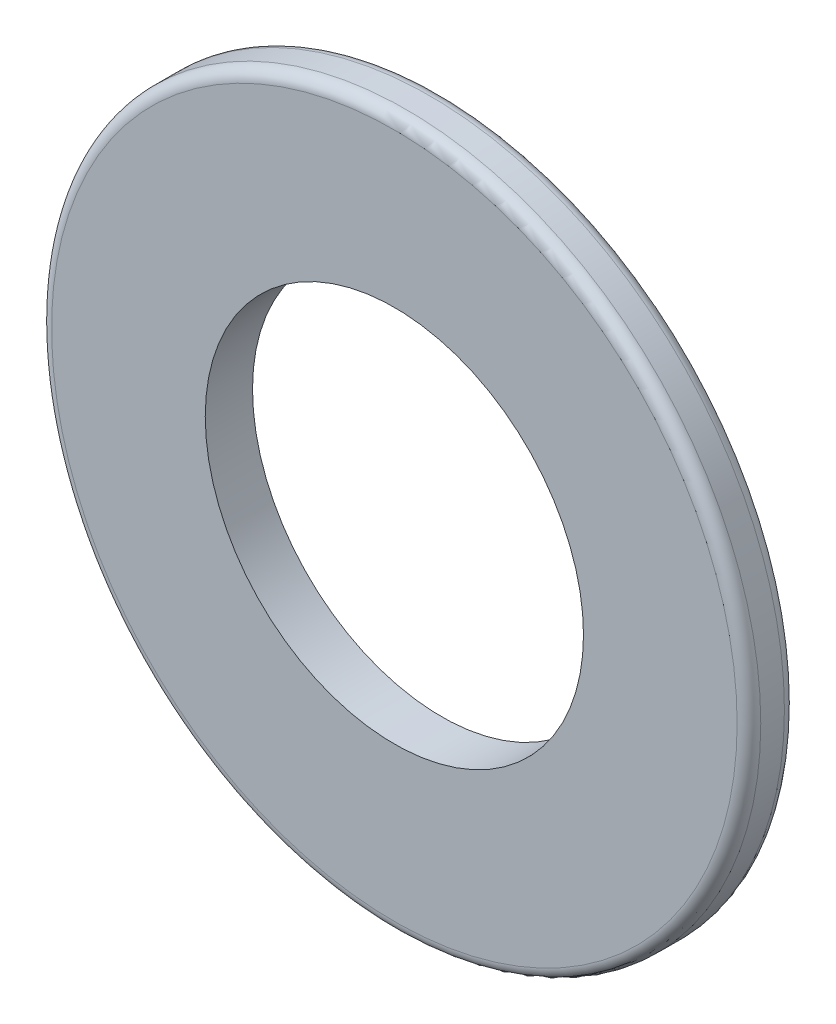
SolidWorks part; units mm, degrees
ref_plane "Front Plane" through (0, 0, 0) normal (0, 0, 1) x (1, 0, 0)
ref_plane "Top Plane" through (0, 0, 0) normal (0, 1, 0) x (1, 0, 0)
ref_plane "Right Plane" through (0, 0, 0) normal (1, 0, 0) x (0, 0, -1)
sketch "Sketch1" plane through (0, 0, 0) normal (0, 0, 1) x (1, 0, 0)
  circle A0 centre (0, 0) radius 4
  circle A1 centre (0, 0) radius 7.5
extrude "Boss-Extrude1" add sketch "Sketch1" along normal blind 1
fillet "Fillet1" radius 0.25 2 edges at (7.5, 0, 0) (7.5, 0, 1)
